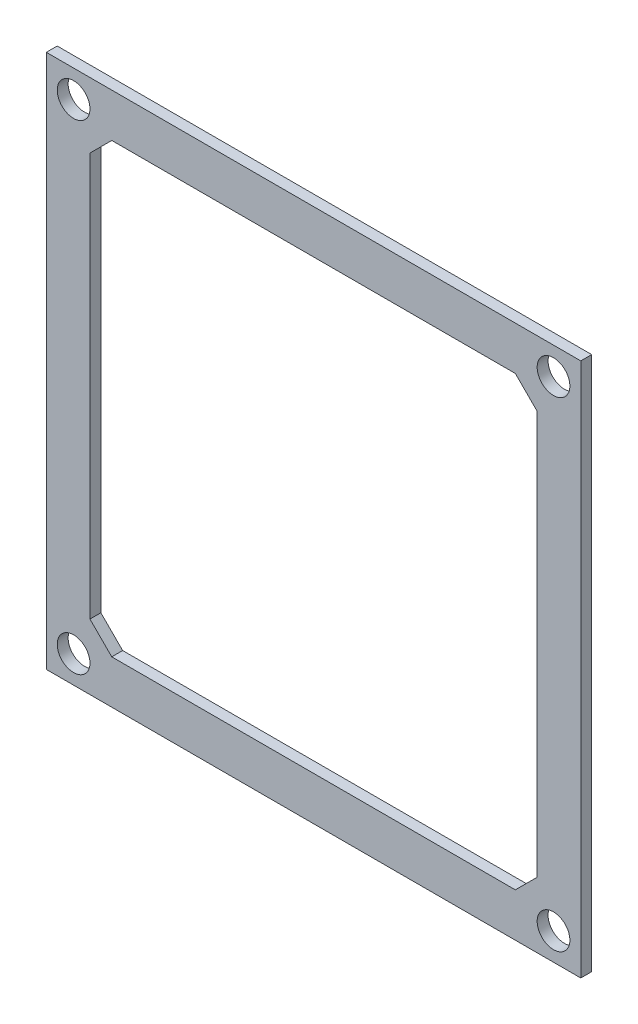
SolidWorks part; units mm, degrees
ref_plane "Alzado" through (0, 0, 0) normal (0, 0, 1) x (1, 0, 0)
ref_plane "Planta" through (0, 0, 0) normal (0, 1, 0) x (1, 0, 0)
ref_plane "Vista lateral" through (0, 0, 0) normal (1, 0, 0) x (0, 0, -1)
sketch "Croquis1" plane through (0, 0, 0) normal (0, 0, 1) x (1, 0, 0)
  line L0 (-61.0766, 25.6979) -> (-61.0766, -15.3021) construction
  line L1 (-65.0766, 29.6979) -> (-16.0766, 29.6979)
  line L2 (-65.0766, 29.6979) -> (-65.0766, -19.3021)
  line L3 (-65.0766, -19.3021) -> (-16.0766, -19.3021)
  line L4 (-16.0766, 29.6979) -> (-16.0766, -19.3021)
  line L5 (-61.0766, -15.3021) -> (-20.0766, -15.3021) construction
  line L6 (-20.0766, -15.3021) -> (-20.0766, 25.6979) construction
  line L7 (-20.0766, 25.6979) -> (-61.0766, 25.6979) construction
  line L8 (-61.0766, 25.6979) -> (-61.0766, 23.6979) construction
  line L9 (-61.0766, 23.6979) -> (-61.0766, -13.3021)
  line L10 (-59.0766, -15.3021) -> (-22.0766, -15.3021)
  line L11 (-61.0766, -13.3021) -> (-59.0766, -15.3021)
  line L12 (-22.0766, -15.3021) -> (-20.0766, -13.3021)
  line L13 (-20.0766, -13.3021) -> (-20.0766, 23.6979)
  line L14 (-20.0766, 23.6979) -> (-22.0766, 25.6979)
  line L15 (-22.0766, 25.6979) -> (-59.0766, 25.6979)
  line L16 (-59.0766, 25.6979) -> (-61.0766, 23.6979)
  circle A0 centre (-62.5766, 27.1979) radius 1.5
  circle A1 centre (-18.5766, 27.1979) radius 1.5
  circle A2 centre (-18.5766, -16.8021) radius 1.5
  circle A3 centre (-62.5766, -16.8021) radius 1.5
  dimension "D8" = 2.5
  dimension "D1" = 49
  dimension "D2" = 49
  dimension "D3" = 4
  dimension "D4" = 4
  dimension "D5" = 4
  dimension "D6" = 4
  dimension "D7" = 2
  dimension "D9" = 2.5
  dimension "D10" = 2
  dimension "D11" = 2
extrude "Saliente-Extruir1" add sketch "Croquis1" along normal blind 1
